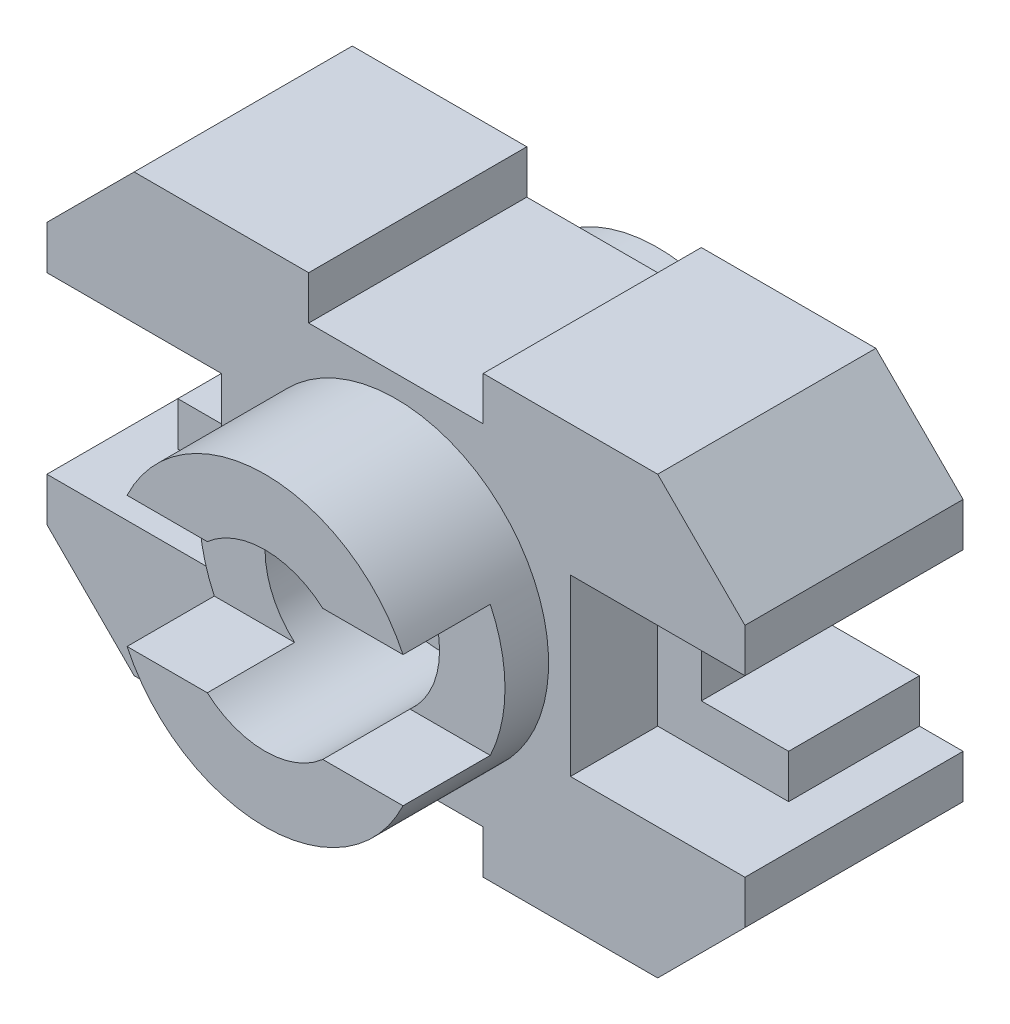
SolidWorks part; units mm, degrees
ref_plane "Front Plane" through (0, 0, 0) normal (0, 0, 1) x (1, 0, 0)
ref_plane "Top Plane" through (0, 0, 0) normal (0, 1, 0) x (1, 0, 0)
ref_plane "Right Plane" through (0, 0, 0) normal (1, 0, 0) x (0, 0, -1)
sketch "Sketch1" plane through (0, 0, 0) normal (0, 0, 1) x (1, 0, 0)
  line L1 (0, 0) -> (160, 0)
  line L2 (0, 0) -> (0, 100)
  line L3 (0, 100) -> (160, 100)
  line L4 (160, 0) -> (160, 100)
  dimension "D1" = 100
  dimension "D2" = 160
extrude "Boss-Extrude2" add sketch "Sketch1" along normal blind 50
sketch "Sketch4" plane through (0, 0, 50) normal (0, 0, 1) x (1, 0, 0)
  line L0 (0, 80) -> (20, 100)
  line L1 (0, 100) -> (0, 0) construction
  line L2 (160, 100) -> (0, 100) construction
  line L3 (20, 100) -> (0, 100)
  line L4 (0, 100) -> (0, 80)
  line L5 (0, 20) -> (20, 0)
  line L6 (0, 0) -> (160, 0) construction
  line L7 (20, 0) -> (0, 0)
  line L8 (0, 0) -> (0, 20)
  line L9 (140, 100) -> (160, 80)
  line L10 (160, 0) -> (160, 100) construction
  line L11 (160, 80) -> (160, 100)
  line L12 (160, 100) -> (140, 100)
  line L13 (160, 20) -> (140, 0)
  line L14 (140, 0) -> (160, 0)
  line L15 (160, 0) -> (160, 20)
  dimension "D1" = 20
  dimension "D2" = 20
  dimension "D3" = 20
  dimension "D4" = 20
  dimension "D5" = 20
  dimension "D6" = 20
  dimension "D7" = 20
  dimension "D8" = 20
extrude "Cut-Extrude2" cut sketch "Sketch4" against normal blind 50
sketch "Sketch5" plane through (0, 0, 50) normal (0, 0, 1) x (1, 0, 0)
  line L0 (0, 70) -> (10, 70)
  line L1 (0, 80) -> (0, 20) construction
  line L2 (10, 70) -> (10, 60)
  line L3 (10, 60) -> (30, 60)
  line L4 (30, 60) -> (30, 40)
  line L5 (30, 40) -> (10, 40)
  line L6 (10, 40) -> (10, 30)
  line L7 (10, 30) -> (0, 30)
  line L8 (160, 70) -> (150, 70)
  line L9 (160, 20) -> (160, 80) construction
  line L10 (150, 70) -> (150, 60)
  line L11 (150, 60) -> (130, 60)
  line L12 (130, 60) -> (130, 40)
  line L13 (130, 40) -> (150, 40)
  line L14 (150, 40) -> (150, 30)
  line L15 (150, 30) -> (160, 30)
  line L16 (160, 70) -> (160, 30)
  line M3 (160, 20) -> (160, 80)
  line M7 (0, 80) -> (0, 20)
  dimension "D1" = 10
  dimension "D2" = 10
  dimension "D3" = 10
  dimension "D4" = 10
  dimension "D5" = 10
  dimension "D6" = 10
  dimension "D7" = 20
  dimension "D8" = 20
  dimension "D9" = 10
  dimension "D10" = 10
  dimension "D11" = 10
  dimension "D12" = 10
  dimension "D13" = 10
  dimension "D14" = 10
extrude "Cut-Extrude3" cut sketch "Sketch5" against normal blind 50 contours L7 L6 L5 L4 L3 L2 L0 M7 | L14 L15 L8 L10 L11 L12 L13 M3
sketch "Sketch6" plane through (0, 0, 50) normal (0, 0, 1) x (1, 0, 0)
  line L0 (10, 70) -> (40, 70)
  line L1 (40, 70) -> (40, 30)
  line L2 (10, 30) -> (40, 30)
  line L3 (10, 70) -> (10, 60)
  line L4 (10, 60) -> (30, 60)
  line L5 (30, 60) -> (30, 40)
  line L6 (30, 40) -> (10, 40)
  line L7 (10, 40) -> (10, 30)
  dimension "D1" = 30
extrude "Cut-Extrude4" cut sketch "Sketch6" against normal blind 20
sketch "Sketch7" plane through (0, 0, 50) normal (0, 0, 1) x (1, 0, 0)
  line L0 (150, 70) -> (120, 70)
  line L1 (120, 70) -> (120, 30)
  line L2 (150, 30) -> (120, 30)
  line L3 (150, 70) -> (150, 60)
  line L4 (150, 60) -> (130, 60)
  line L5 (130, 60) -> (130, 40)
  line L6 (130, 40) -> (150, 40)
  line L7 (150, 40) -> (150, 30)
  dimension "D1" = 30
extrude "Cut-Extrude5" cut sketch "Sketch7" against normal blind 20
sketch "Sketch8" plane through (0, 0, 50) normal (0, 0, 1) x (1, 0, 0)
  line L0 (140, 100) -> (20, 100) construction
  line L1 (100, 100) -> (60, 100)
  line L2 (100, 100) -> (100, 90)
  line L3 (100, 90) -> (60, 90)
  line L4 (60, 100) -> (60, 90)
  line L5 (20, 0) -> (140, 0) construction
  line L6 (100, 0) -> (60, 0)
  line L7 (100, 0) -> (100, 10)
  line L8 (100, 10) -> (60, 10)
  line L9 (60, 0) -> (60, 10)
  dimension "D1" = 40
  dimension "D2" = 40
  dimension "D3" = 10
  dimension "D4" = 10
  dimension "D5" = 20
  dimension "D6" = 20
extrude "Cut-Extrude6" cut sketch "Sketch8" against normal blind 125
sketch "Sketch9" plane through (0, 0, 0) normal (0, 0, -1) x (-1, 0, 0)
  circle A0 centre (-80, 50) radius 35
  dimension "D1" = 70
  dimension "D2" = 80
  dimension "D3" = 40
extrude "Boss-Extrude3" add sketch "Sketch9" along normal blind 10
sketch "Sketch10" plane through (0, 0, -10) normal (0, 0, -1) x (-1, 0, 0)
  circle A0 centre (-80, 50) radius 15
  dimension "D1" = 30
extrude "Cut-Extrude8" cut sketch "Sketch10" against normal blind 123
sketch "Sketch11" plane through (0, 0, 50) normal (0, 0, 1) x (1, 0, 0)
  circle A0 centre (80, 50) radius 35
  dimension "D1" = 70
extrude "Boss-Extrude4" add sketch "Sketch11" along normal blind 30
sketch "Sketch12" plane through (0, 0, 50) normal (0, 0, -1) x (-1, 0, 0)
  circle A0 centre (-80, 50) radius 15
  dimension "D1" = 30
extrude "Cut-Extrude9" cut sketch "Sketch12" against normal blind 30
sketch "Sketch13" plane through (0, 0, 80) normal (0, 0, 1) x (1, 0, 0)
  circle A0 centre (80, 50) radius 20
  dimension "D1" = 40
extrude "Cut-Extrude10" cut sketch "Sketch13" against normal blind 30
sketch "Sketch14" plane through (0, 0, 80) normal (0, 0, 1) x (1, 0, 0)
  line L0 (66.7712, 65) -> (48.3772, 65)
  line L1 (66.7712, 35) -> (48.3772, 35)
  line L2 (93.2288, 65) -> (111.6228, 65)
  line L3 (93.2288, 35) -> (111.6228, 35)
  circle A0 centre (80, 50) radius 20
  circle A2 centre (80, 50) radius 35
  circle M1 centre (80, 50) radius 20
  circle M2 centre (80, 50) radius 35
  dimension "D1" = 70
  dimension "D2" = 40
  dimension "D3" = 15
  dimension "D4" = 15
  dimension "D5" = 15
  dimension "D6" = 15
extrude "Cut-Extrude11" cut sketch "Sketch14" against normal blind 20 contours L1 L0 M1 M2 | L3 L2 M1 M2
sketch "Sketch15" plane through (0, 0, 50) normal (0, 0, 1) x (1, 0, 0)
  circle A0 centre (80, 50) radius 20
  circle A1 centre (80, 50) radius 15
  dimension "D1" = 30
  dimension "D2" = 40
extrude "Cut-Extrude12" cut sketch "Sketch15" against normal blind 10
